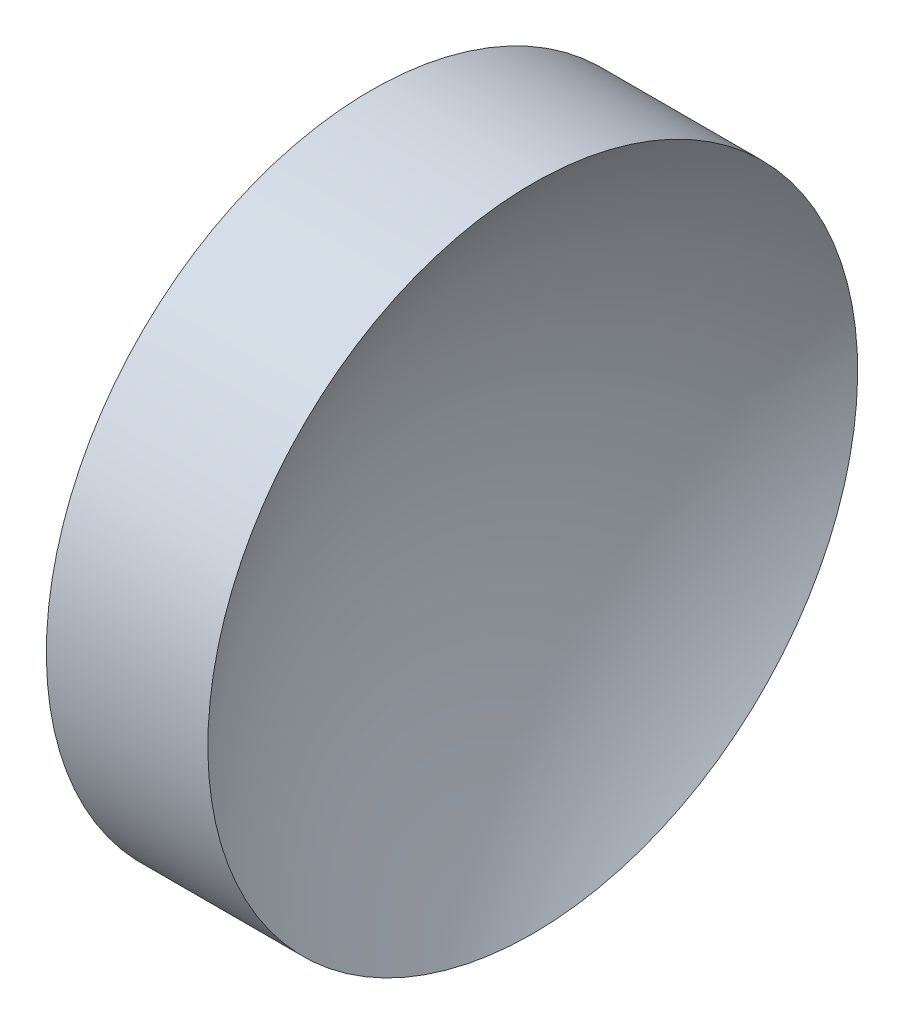
SolidWorks part; units mm, degrees
ref_plane "前视基准面" through (0, 0, 0) normal (0, 0, 1) x (1, 0, 0)
ref_plane "上视基准面" through (0, 0, 0) normal (0, 1, 0) x (1, 0, 0)
ref_plane "右视基准面" through (0, 0, 0) normal (1, 0, 0) x (0, 0, -1)
sketch "草图1" plane through (0, 0, 0) normal (0, 0, 1) x (1, 0, 0)
  line L0 (55.0074, 32.5787) -> (69.3049, 32.5787) construction
  line L1 (57.3582, 32.5787) -> (57.3582, 45.0787)
  line L2 (59.3582, 32.5787) -> (57.3582, 32.5787)
  line L3 (57.3582, 45.0787) -> (63.5713, 45.0787)
  arc A0 (63.5713, 45.0787) -> (59.3582, 32.5787) centre (80.0082, 32.5787) ccw
revolve "旋转1" add sketch "草图1" angle 360 about L0
